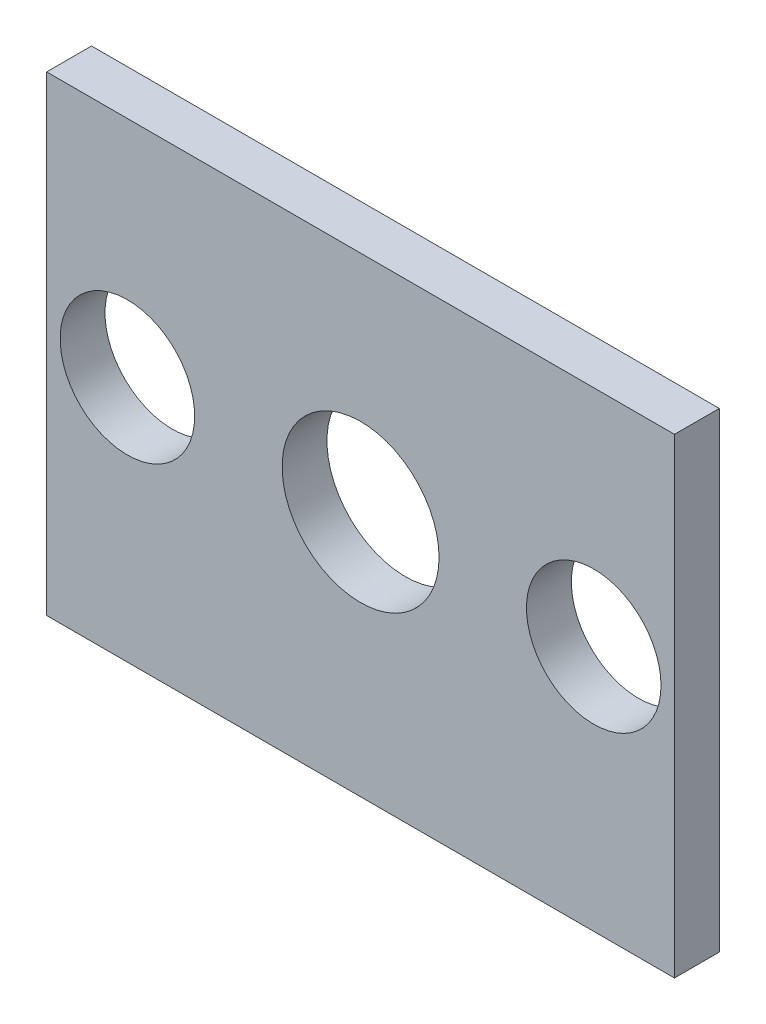
SolidWorks part; units mm, degrees
material "6061-T6 (SS)"
ref_plane "Front Plane" through (0, 0, 0) normal (0, 0, 1) x (1, 0, 0)
ref_plane "Top Plane" through (0, 0, 0) normal (0, 1, 0) x (1, 0, 0)
ref_plane "Right Plane" through (0, 0, 0) normal (1, 0, 0) x (0, 0, -1)
sketch "Sketch1" plane through (0, 0, 0) normal (0, 0, 1) x (1, 0, 0)
  line L1 (-44.45, 31.75) -> (44.45, 31.75)
  line L2 (-44.45, 31.75) -> (-44.45, -34.925)
  line L3 (-44.45, -34.925) -> (44.45, -34.925)
  line L4 (44.45, 31.75) -> (44.45, -34.925)
  circle A0 centre (-33.02, 0) radius 9.525
  circle A1 centre (0, 0) radius 11.1125
  circle A2 centre (33.02, 0) radius 9.525
  circle A3 centre (-33.02, 0) radius 31.75 construction
  circle A4 centre (33.02, 0) radius 31.75 construction
  dimension "D1" = 33.02
  dimension "D3" = 22.225
  dimension "D4" = 19.05
  dimension "D5" = 63.5
  dimension "D6" = 3.175
  dimension "D7" = 44.45
  dimension "D8" = 44.45
  dimension "D2" = 33.02
  dimension "D9" = 66.675
extrude "Boss-Extrude1" add sketch "Sketch1" along normal blind 6.35
sketch "Sketch2" plane through (0, 0, 6.35) normal (0, 0, 1) x (1, 0, 0)
  circle A0 centre (-33.02, 0) radius 9.525
  circle A1 centre (33.02, 0) radius 9.525
  dimension "D1" = 19.05
